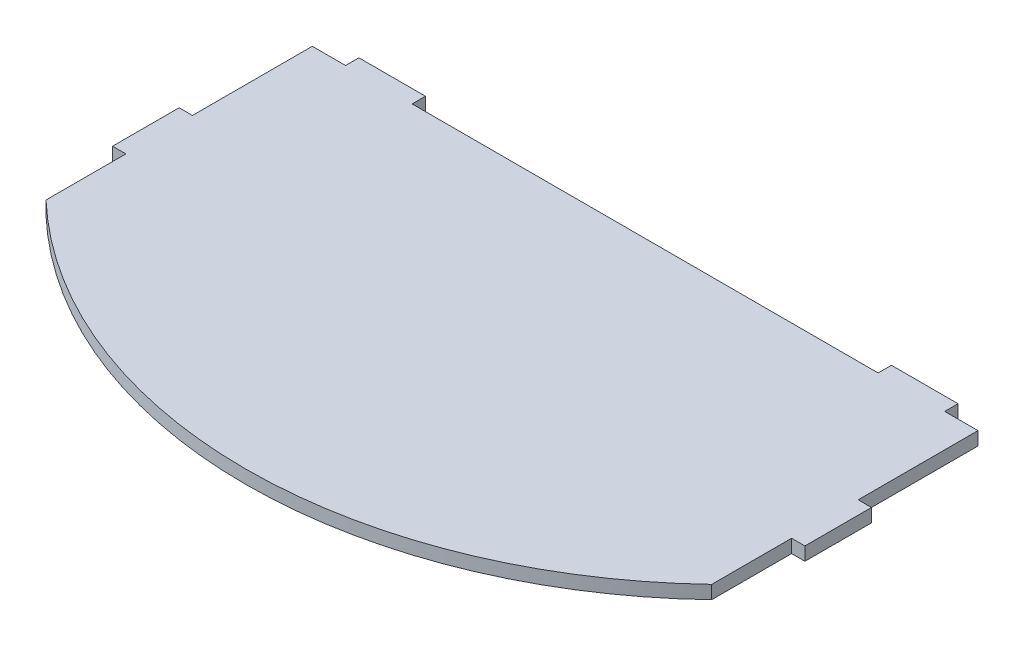
SolidWorks part; units mm, degrees
ref_plane "Přední rovina" through (0, 0, 0) normal (0, 0, 1) x (1, 0, 0)
ref_plane "Horní rovina" through (0, 0, 0) normal (0, 1, 0) x (1, 0, 0)
ref_plane "Pravá rovina" through (0, 0, 0) normal (1, 0, 0) x (0, 0, -1)
sketch "Sketch1" plane through (0, 0, 0) normal (0, 1, 0) x (1, 0, 0)
  line L1 (-100, 60) -> (100, 60)
  line L2 (-100, 60) -> (-100, -60)
  line L3 (-100, -60) -> (100, -60)
  line L4 (100, 60) -> (100, -60)
  line L5 (-100, 60) -> (100, -60) construction
  line L6 (-100, -60) -> (100, 60) construction
  line L7 (-100, 24) -> (-104, 24)
  line L8 (-100, 24) -> (-100, 4)
  line L9 (-100, 4) -> (-104, 4)
  line L10 (-104, 24) -> (-104, 4)
  line L11 (-90, 60) -> (-70, 60)
  line L12 (-90, 60) -> (-90, 64)
  line L13 (-90, 64) -> (-70, 64)
  line L14 (-70, 60) -> (-70, 64)
  line L15 (-10, 60) -> (10, 60)
  line L16 (-10, 60) -> (-10, 64)
  line L17 (-10, 64) -> (10, 64)
  line L18 (10, 60) -> (10, 64)
  line L19 (70, 60) -> (90, 60)
  line L20 (70, 60) -> (70, 64)
  line L21 (70, 64) -> (90, 64)
  line L22 (90, 60) -> (90, 64)
  line L23 (0, -44.8063) -> (0, 63.4683) construction
  line L24 (104, 24) -> (104, 4)
  line L25 (100, 4) -> (104, 4)
  line L26 (100, 24) -> (100, 4)
  line L27 (100, 24) -> (104, 24)
  line L28 (-55, 60) -> (-25, 60)
  line L29 (-55, 60) -> (-55, 50)
  line L30 (-55, 50) -> (-25, 50)
  line L31 (-25, 60) -> (-25, 50)
  line L32 (55, 60) -> (25, 60)
  line L33 (55, 60) -> (55, 50)
  line L34 (55, 50) -> (25, 50)
  line L35 (25, 60) -> (25, 50)
  arc A0 (100, -20) -> (-100, -20) centre (0, 85) cw
  point P0 (0, 0)
  point P39 (100, 0)
  point P40 (0, 0)
  point P41 (0, 0)
  dimension "D15" = 80
  dimension "D1" = 200
  dimension "D2" = 120
  dimension "D3" = 4
  dimension "D4" = 4
  dimension "D5" = 20
  dimension "D6" = 60
  dimension "D7" = 60
  dimension "D8" = 36
  dimension "D9" = 30
  dimension "D10" = 10
  dimension "D11" = 30
  dimension "D12" = 10
  dimension "D13" = 15
  dimension "D14" = 15
  dimension "D16" = 80
extrude "Extrude1" add sketch "Sketch1" along normal blind 4 contours L4 L1 L2 L3 | L1 L14 L13 L12 | L1 L22 L21 L20 | L31 L1 L29 L30 | L1 L35 L34 L33 | L10 L9 L8 L7 | L24 L25 L26 L27
